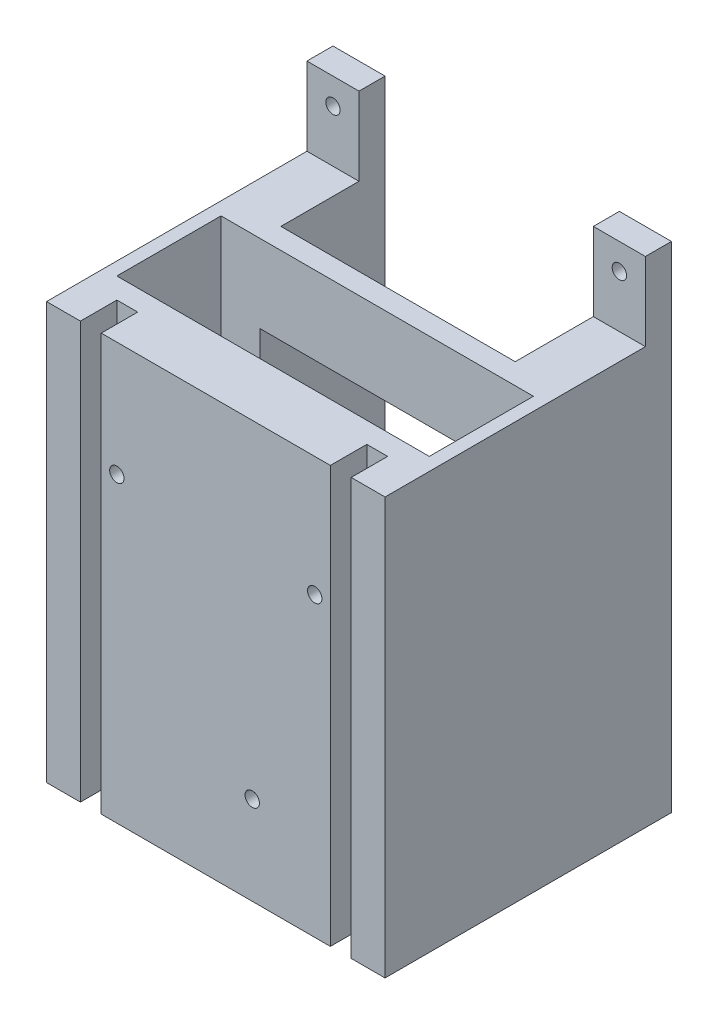
SolidWorks part; units mm, degrees
ref_plane "Front Plane" through (0, 0, 0) normal (0, 0, 1) x (1, 0, 0)
ref_plane "Top Plane" through (0, 0, 0) normal (0, 1, 0) x (1, 0, 0)
ref_plane "Right Plane" through (0, 0, 0) normal (1, 0, 0) x (0, 0, -1)
sketch "Sketch1" plane through (0, 0, 0) normal (0, 0, 1) x (1, 0, 0)
  line L0 (41.275, 19.05) -> (41.275, 152.4) construction
  line L1 (-41.275, 139.7) -> (41.275, 139.7)
  line L2 (-41.275, 139.7) -> (-41.275, 19.05)
  line L3 (-41.275, 19.05) -> (41.275, 19.05)
  line L4 (41.275, 139.7) -> (41.275, 19.05)
  line L5 (-41.275, 139.7) -> (41.275, 19.05) construction
  line L6 (-41.275, 19.05) -> (41.275, 139.7) construction
  point P0 (0, 79.375)
  dimension "D1" = 120.65
  dimension "D2" = 82.55
extrude "Boss-Extrude1" add sketch "Sketch1" along normal blind 69.85
sketch "Sketch2" plane through (0, 139.7, 0) normal (0, 1, 0) x (1, 0, 0)
  line L0 (-38.1, -30.48) -> (38.1, -30.48)
  line L1 (38.1, -30.48) -> (38.1, -55.88)
  line L2 (38.1, -55.88) -> (-38.1, -55.88)
  line L3 (-38.1, -55.88) -> (-38.1, -30.48)
  line L4 (41.275, -69.85) -> (-41.275, -69.85) construction
  point P8 (0, -30.48)
  dimension "D1" = 76.2
  dimension "D2" = 25.4
  dimension "D3" = 13.97
extrude "Cut-Extrude1" cut sketch "Sketch2" against normal blind 107.95
sketch "Sketch3" plane through (0, 0, 69.85) normal (0, 0, 1) x (1, 0, 0)
  line L0 (33.02, 19.05) -> (33.02, 120.65)
  line L1 (-41.275, 19.05) -> (41.275, 19.05) construction
  line L2 (33.02, 120.65) -> (27.94, 120.65)
  line L3 (27.94, 120.65) -> (27.94, 19.05)
  line L4 (27.94, 19.05) -> (33.02, 19.05)
  line L6 (0, 139.7) -> (0, 19.05) construction
  line L7 (41.275, 139.7) -> (-41.275, 139.7) construction
  dimension "D1" = 27.94
  dimension "D2" = 101.6
  dimension "D3" = 5.08
extrude "Cut-Extrude2" cut sketch "Sketch3" against normal blind 8.89
mirror "Mirror1" about plane through (0, 0, 0) normal (1, 0, 0) of "Cut-Extrude2"
sketch "Sketch4" plane through (-41.275, 0, 0) normal (-1, 0, 0) x (0, 0, 1)
  line L0 (69.85, 139.7) -> (6.35, 139.7)
  line L1 (69.85, 139.7) -> (0, 139.7) construction
  line L2 (6.35, 139.7) -> (6.35, 120.65)
  line L3 (6.35, 120.65) -> (69.85, 120.65)
  line L5 (69.85, 120.65) -> (69.85, 139.7)
  line L6 (69.85, 139.7) -> (69.85, 19.05) construction
  line L7 (0, 139.7) -> (0, 19.05) construction
  dimension "D1" = 19.05
  dimension "D2" = 6.35
extrude "Cut-Extrude3" cut sketch "Sketch4" against normal through all
sketch "Sketch5" plane through (0, 139.7, 0) normal (0, 1, 0) x (1, 0, 0)
  line L0 (-28.575, 0) -> (28.575, 0)
  line L1 (41.275, 0) -> (-41.275, 0) construction
  line L2 (28.575, 0) -> (28.575, -25.4)
  line L3 (28.575, -25.4) -> (-28.575, -25.4)
  line L5 (-28.575, -25.4) -> (-28.575, 0)
  point P9 (0, 0)
  dimension "D1" = 57.15
  dimension "D2" = 25.4
extrude "Cut-Extrude4" cut sketch "Sketch5" against normal through all
hole_wizard "#40 (0.138) Diameter Hole1" positions "Sketch11" profile "Sketch9" hole size "#40" standard "ANSI Inch" end condition up to next
sketch "Sketch11" plane through (0, 0, 69.85) normal (0, 0, 1) x (1, 0, 0)
  point P0 (-24.13, 92.72)
  point P3 (24.13, 91.45)
  point P6 (8.89, 40.65)
sketch "Sketch9" plane through (-24.13, 92.72, 69.85) normal (1, 0, 0) x (0, -1, 0)
  line L0 (0, 0) -> (0, 13.97)
  line L1 (0, 13.97) -> (1.7526, 13.97)
  line L2 (1.7526, 13.97) -> (1.7526, 0)
  line L5 (1.7526, 0) -> (0, 0)
  line L11 (0, -6.35) -> (0, 107.95) construction
  dimension "Thru Hole Dia." = 3.5052
  dimension "Thru Hole Depth" = 13.97
sketch "Sketch14" plane through (0, 19.05, 0) normal (0, -1, 0) x (1, 0, 0)
  line L0 (-41.275, 69.85) -> (-33.02, 69.85)
  line L1 (-33.02, 69.85) -> (-33.02, 60.96)
  line L2 (-33.02, 60.96) -> (-27.94, 60.96)
  line L3 (-27.94, 60.96) -> (-27.94, 69.85)
  line L4 (-27.94, 69.85) -> (27.94, 69.85)
  line L5 (27.94, 69.85) -> (27.94, 60.96)
  line L6 (27.94, 60.96) -> (33.02, 60.96)
  line L7 (33.02, 60.96) -> (33.02, 69.85)
  line L8 (33.02, 69.85) -> (41.275, 69.85)
  line L9 (41.275, 69.85) -> (41.275, 0)
  line L10 (41.275, 0) -> (28.575, 0)
  line L11 (28.575, 0) -> (28.575, 25.4)
  line L12 (28.575, 25.4) -> (-28.575, 25.4)
  line L13 (-28.575, 25.4) -> (-28.575, 0)
  line L14 (-28.575, 0) -> (-41.275, 0)
  line L15 (-41.275, 0) -> (-41.275, 69.85)
extrude "Boss-Extrude2" add sketch "Sketch14" along normal blind 6.35
sketch "Sketch15" plane through (0, 0, 25.4) normal (0, 0, -1) x (-1, 0, 0)
  line L0 (-28.575, 101.6) -> (28.575, 101.6)
  line L1 (28.575, 101.6) -> (28.575, 12.7)
  line L2 (28.575, 12.7) -> (-28.575, 12.7)
  line L3 (-28.575, 12.7) -> (-28.575, 101.6)
  line L6 (28.575, 12.7) -> (-28.575, 12.7) construction
  line L7 (28.575, 12.7) -> (28.575, 139.7) construction
  line L8 (28.575, 12.7) -> (28.575, 120.65) construction
  line L9 (-28.575, 12.7) -> (-28.575, 120.65) construction
  line L10 (-28.575, 12.7) -> (-28.575, 139.7) construction
  dimension "D1" = 88.9
extrude "Cut-Extrude5" cut sketch "Sketch15" against normal blind 12.7
sketch "Sketch16" plane through (41.275, 0, 0) normal (1, 0, 0) x (0, 0, -1)
  line L0 (-69.85, 12.7) -> (0, 12.7)
  line L1 (0, 12.7) -> (0, 19.05)
  line L2 (0, 19.05) -> (-69.85, 19.05)
  line L3 (-69.85, 12.7) -> (-69.85, 120.65) construction
  line L4 (-69.85, 19.05) -> (-69.85, 12.7)
  dimension "D1" = 6.35
extrude "Cut-Extrude6" cut sketch "Sketch16" against normal through all
sketch "Sketch17" plane through (0, 0, 6.35) normal (0, 0, 1) x (1, 0, 0)
  line L0 (-34.925, 139.7) -> (-34.925, 120.65) construction
  line L1 (-28.575, 139.7) -> (-41.275, 139.7) construction
  line L2 (-28.575, 120.65) -> (-41.275, 120.65) construction
  circle A0 centre (-34.925, 133.35) radius 1.7526
  dimension "D2" = 3.5052
  dimension "D1" = 6.35
extrude "Cut-Extrude7" cut sketch "Sketch17" against normal up to next (6.35 mm away)
mirror "Mirror2" about plane through (0, 0, 0) normal (1, 0, 0) of "Cut-Extrude7"
